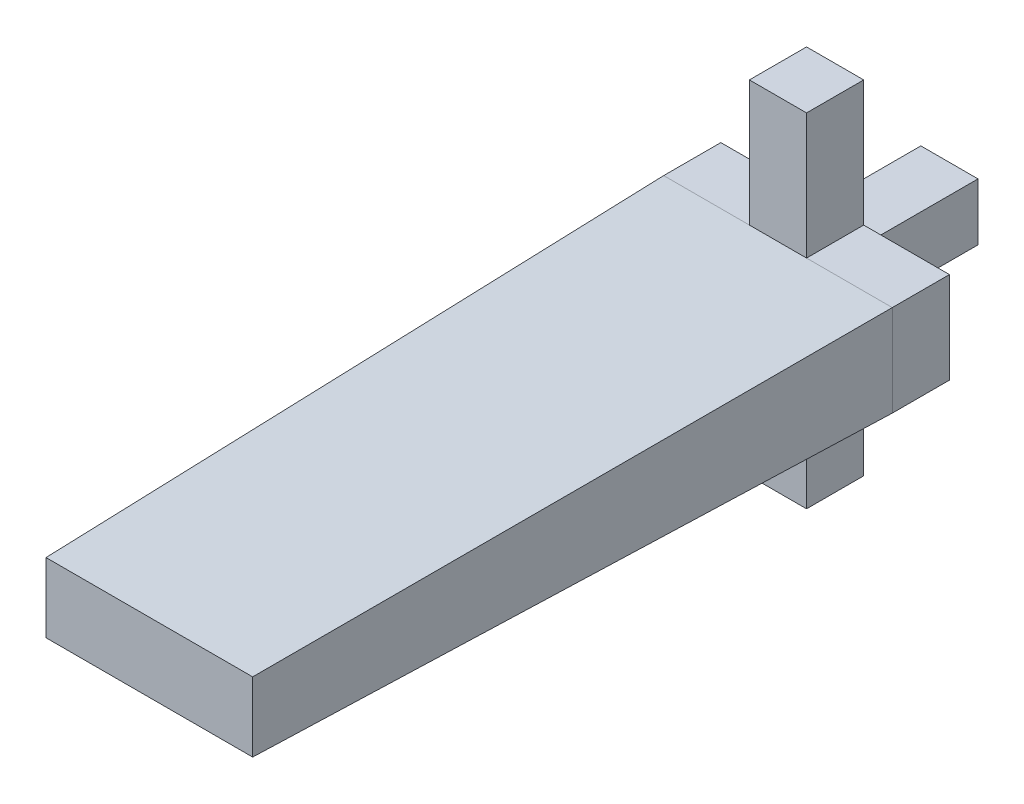
SolidWorks part; units mm, degrees
ref_plane "正面" through (0, 0, 0) normal (0, 0, 1) x (1, 0, 0)
ref_plane "平面" through (0, 0, 0) normal (0, 1, 0) x (1, 0, 0)
ref_plane "右側面" through (0, 0, 0) normal (1, 0, 0) x (0, 0, -1)
sketch "ｽｹｯﾁ1" plane through (0, 0, 0) normal (0, 0, 1) x (1, 0, 0)
  line L1 (-10, 4) -> (10, 4)
  line L2 (-10, 4) -> (-10, -4)
  line L3 (-10, -4) -> (10, -4)
  line L4 (10, 4) -> (10, -4)
  line L5 (-10, 4) -> (10, -4) construction
  line L6 (-10, -4) -> (10, 4) construction
  point P0 (0, 0)
  dimension "D1" = 8
  dimension "D2" = 20
extrude "ﾎﾞｽ - 押し出し1" add sketch "ｽｹｯﾁ1" along normal blind 5
sketch "ｽｹｯﾁ5" plane through (0, 0, 0) normal (0, 0, -1) x (-1, 0, 0)
  line L1 (-2.5, -2.5) -> (2.5, -2.5)
  line L2 (-2.5, -2.5) -> (-2.5, 2.5)
  line L3 (-2.5, 2.5) -> (2.5, 2.5)
  line L4 (2.5, -2.5) -> (2.5, 2.5)
  line L5 (-2.5, -2.5) -> (2.5, 2.5) construction
  line L6 (-2.5, 2.5) -> (2.5, -2.5) construction
  point P0 (0, 0)
  dimension "D1" = 5
  dimension "D2" = 5
extrude "ﾎﾞｽ - 押し出し5" add sketch "ｽｹｯﾁ5" along normal blind 10
sketch "ｽｹｯﾁ8" plane through (0, 0, 5) normal (0, 0, 1) x (1, 0, 0)
  line L1 (10, 4) -> (-10, 4)
  line L2 (10, 4) -> (10, -4)
  line L3 (10, -4) -> (-10, -4)
  line L4 (-10, 4) -> (-10, -4)
extrude "ﾎﾞｽ - 押し出し6" add sketch "ｽｹｯﾁ8" along normal blind 55 draft 1
sketch "ｽｹｯﾁ9" plane through (0, 4, 0) normal (0, 1, 0) x (1, 0, 0)
  line L0 (10, 0) -> (-10, 0) construction
  line L1 (2.5, 0) -> (-2.5, 0)
  line L2 (2.5, 0) -> (2.5, -5)
  line L3 (2.5, -5) -> (-2.5, -5)
  line L4 (-2.5, 0) -> (-2.5, -5)
  line L5 (-10, -5) -> (-10, 0) construction
  dimension "D1" = 5
  dimension "D2" = 5
  dimension "D3" = 7.5
extrude "ﾎﾞｽ - 押し出し7" add sketch "ｽｹｯﾁ9" along normal blind 11
sketch "ｽｹｯﾁ10" plane through (0, -4, 0) normal (0, -1, 0) x (-1, 0, 0)
  line L0 (10, 0) -> (-10, 0) construction
  line L1 (-2.5, 0) -> (2.5, 0)
  line L2 (-2.5, 0) -> (-2.5, -5)
  line L3 (-2.5, -5) -> (2.5, -5)
  line L4 (2.5, 0) -> (2.5, -5)
  line L5 (10, -5) -> (10, 0) construction
  dimension "D1" = 5
  dimension "D2" = 5
  dimension "D3" = 7.5
extrude "ﾎﾞｽ - 押し出し8" add sketch "ｽｹｯﾁ10" along normal blind 11
